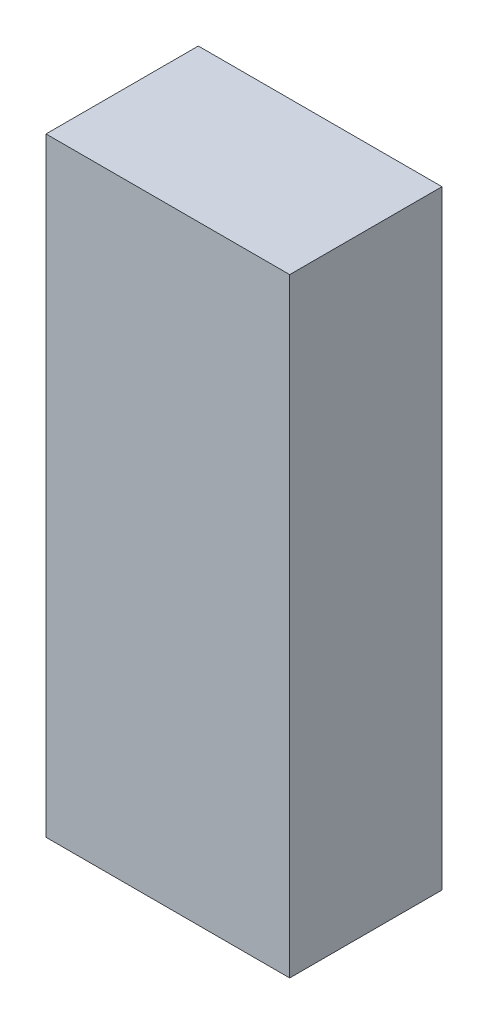
SolidWorks part; units mm, degrees
ref_plane "Front Plane" through (0, 0, 0) normal (0, 0, 1) x (1, 0, 0)
ref_plane "Top Plane" through (0, 0, 0) normal (0, 1, 0) x (1, 0, 0)
ref_plane "Right Plane" through (0, 0, 0) normal (1, 0, 0) x (0, 0, -1)
sketch "Sketch1" plane through (0, 0, 0) normal (0, 0, 1) x (1, 0, 0)
  line L1 (0, 0) -> (7.62, 0)
  line L2 (0, 0) -> (0, 19.05)
  line L3 (0, 19.05) -> (7.62, 19.05)
  line L4 (7.62, 0) -> (7.62, 19.05)
  dimension "D1" = 19.05
  dimension "D2" = 7.62
extrude "Boss-Extrude1" add sketch "Sketch1" along normal blind 4.7625
